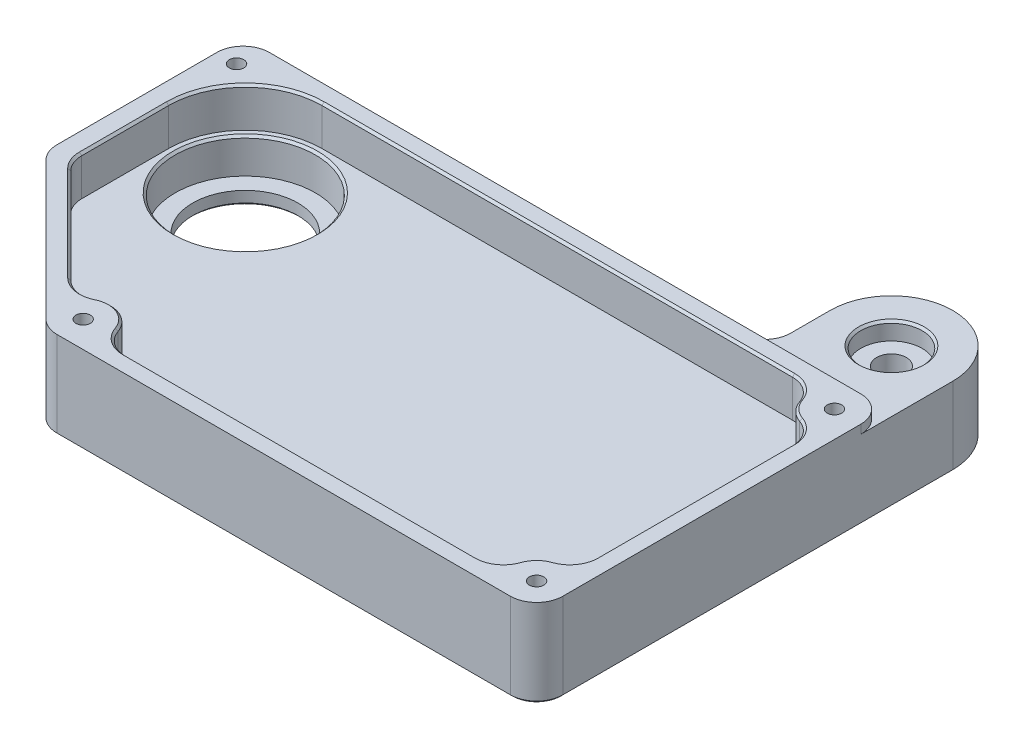
SolidWorks part; units mm, degrees
material "Alumina"
ref_plane "Plan de face" through (0, 0, 0) normal (0, 0, 1) x (1, 0, 0)
ref_plane "Plan de dessus" through (0, 0, 0) normal (0, 1, 0) x (1, 0, 0)
ref_plane "Plan de droite" through (0, 0, 0) normal (1, 0, 0) x (0, 0, -1)
sketch "Sketch2" plane through (0, 0, 0) normal (0, 1, 0) x (1, 0, 0)
  line L0 (-57, 40) -> (62, 40)
  line L1 (90, 55) -> (90, -40)
  line L10 (-22, -40) -> (90, -40)
  line L11 (62, 55) -> (62, 40)
  line L12 (-57, -5) -> (-22, -40)
  line L17 (-57, 40) -> (-57, -5)
  arc A9 (90, 55) -> (62, 55) centre (76, 55) ccw
  circle A10 centre (-35, 18.5) radius 12
  point P0 (-62, -40)
  dimension "D4" = 21.5
  dimension "D5" = 24
  dimension "D6" = 147
  dimension "D9" = 112
  dimension "D1" = 28
  dimension "D3" = 22
  dimension "D2" = 15
  dimension "D7" = 80
  dimension "D8" = 45
extrude "Boss-Extrude1" add sketch "Sketch2" along normal blind 20
fillet "Fillet1" radius 6 5 edges at (90, 10, 40) (62, 10, -40) (-22, 10, 40) (-57, 10, 5) (-57, 10, -40)
hole_wizard "Tap Drill for M4 Tap1" positions "Sketch5" profile "Sketch6" hole size "M4" standard "ISO"
sketch "Sketch5" plane through (0, 20, 0) normal (0, 1, 0) x (1, 0, 0)
  line L0 (-90, 10.5) -> (90, 10.5) construction
  line L1 (90, 55) -> (90, -34) construction
  line L2 (0, 40) -> (0, -40) construction
  line L3 (-51, 40) -> (56, 40) construction
  line L4 (-19.5147, -40) -> (84, -40) construction
  line L5 (90, 55) -> (90, -34) construction
  line L7 (84, 40) -> (-72.5, 40) construction
  line L11 (-57, 34) -> (-57, -2.5147) construction
  arc A10 (84, -40) -> (90, -34) centre (84, -34) ccw construction
  point P12 (-52.5, 34)
  point P16 (84, -34)
  point P18 (84, 34)
  point P108 (-19.5147, -34)
  dimension "D1" = 6
  dimension "D2" = 6
  dimension "D3" = 4.5
sketch "Sketch6" plane through (-19.5147, 20, 34) normal (1, 0, 0) x (0, 0, 1)
  line L0 (0, 0) -> (0, 13.9914)
  line L1 (0, 13.9914) -> (1.65, 13)
  line L2 (1.65, 13) -> (1.65, 0)
  line L5 (1.65, 0) -> (0, 0)
  line L10 (0, 13.9914) -> (-1.65, 13) construction
  line L11 (0, -6.35) -> (0, 107.95) construction
  dimension "Hole Dia." = 3.3
  dimension "Hole Depth" = 13
  dimension "Drill Angle" = 118
sketch "Sketch7" plane through (0, 20, 0) normal (0, 1, 0) x (1, 0, 0)
  line L0 (90, 55) -> (90, -34) construction
  line L1 (-52.5, 18.5) -> (-52.5, -1.3579)
  line L8 (66, 55) -> (66, 46)
  line L10 (-52.4142, -3.9289) -> (-20.9289, -35.4142)
  line L11 (-19.5147, -36) -> (84, -36)
  line L12 (86, -34) -> (86, 55)
  line L13 (56, 36) -> (-51, 36)
  line L14 (-50.7426, -5.6005) -> (-25.116, -31.2272)
  line L16 (-13.5934, -36) -> (78.0786, -36)
  line L17 (86, -28.0786) -> (86, 28.0786)
  line L18 (78.0786, 36) -> (-35, 36)
  line L26 (-53, 34) -> (-53, -2.5147)
  arc A0 (-52.5, -1.3579) -> (-50.7426, -5.6005) centre (-46.5, -1.3579) ccw
  circle A3 centre (84, 34) radius 1.65 construction
  arc A5 (-13.5934, -36) -> (-25.116, -31.2272) centre (-19.5147, -34) ccw
  arc A7 (-35, 36) -> (-52.5, 18.5) centre (-35, 18.5) ccw
  arc A10 (-51, 36) -> (-53, 34) centre (-51, 34) ccw
  arc A11 (84, -36) -> (86, -34) centre (84, -34) ccw
  arc A12 (86, 55) -> (66, 55) centre (76, 55) ccw
  arc A14 (-20.9289, -35.4142) -> (-19.5147, -36) centre (-19.5147, -34) ccw
  arc A22 (56, 36) -> (66, 46) centre (56, 46) ccw
  arc A24 (78.0786, 36) -> (86, 28.0786) centre (84, 34) ccw
  arc A26 (-53, -2.5147) -> (-52.4142, -3.9289) centre (-51, -2.5147) ccw
  arc A30 (86, -28.0786) -> (78.0786, -36) centre (84, -34) ccw
  dimension "D2" = 6
  dimension "D3" = 4
  dimension "D1" = 4
extrude "Cut-Extrude4" cut sketch "Sketch7" against normal blind 9
fillet "Fillet2" radius 6 6 edges at (86, 15.5, -28.0786) (78.0786, 15.5, -36) (86, 15.5, 28.0786) (78.0786, 15.5, 36) (-25.116, 15.5, 31.2272) (-13.5934, 15.5, 36)
sketch "Sketch8" plane through (0, 11, 0) normal (0, 1, 0) x (1, 0, 0)
  circle A0 centre (-35, 18.5) radius 16
  dimension "D1" = 32
extrude "Cut-Extrude5" cut sketch "Sketch8" against normal blind 8
hole_wizard "Tap Drill for M8 Tap1" positions "Sketch10" profile "Sketch11" hole size "M8" standard "ISO" end condition through all
sketch "Sketch10" plane through (0, 20, 0) normal (0, 1, 0) x (1, 0, 0)
  point P0 (76, 55)
sketch "Sketch11" plane through (76, 20, -55) normal (1, 0, 0) x (0, 0, 1)
  line L0 (0, 0) -> (0, 20)
  line L1 (0, 20) -> (3.4, 20)
  line L2 (3.4, 20) -> (3.4, 0)
  line L5 (3.4, 0) -> (0, 0)
  line L11 (0, -6.35) -> (0, 107.95) construction
  dimension "Thru Hole Dia." = 6.8
  dimension "Thru Hole Depth" = 20
sketch "Sketch12" plane through (0, 20, 0) normal (0, 1, 0) x (1, 0, 0)
  line L0 (84, 40) -> (50.8588, 40)
  line L2 (50.8588, 55) -> (50.8588, 40)
  line L3 (90, 34) -> (101.1412, 34)
  line L4 (101.1412, 55) -> (101.1412, 34)
  arc A1 (90, 34) -> (84, 40) centre (84, 34) ccw
  arc A2 (101.1412, 55) -> (50.8588, 55) centre (76, 55) ccw
extrude "Cut-Extrude6" cut sketch "Sketch12" against normal blind 2
sketch "Sketch13" plane through (0, 18, 0) normal (0, 1, 0) x (1, 0, 0)
  circle A0 centre (76, 55) radius 7
  dimension "D1" = 14
extrude "Cut-Extrude7" cut sketch "Sketch13" against normal blind 4
chamfer "Chamfer1" distance 0.5 angle 45 14 edges at (76, 0, -51.6) (-35, 0, -6.5) (32.2426, 0, 40) (-21.8108, 0, 39.5433) (88.2426, 0, 38.2426) (-39.5, 0, 22.5) (90, 0, -10.5) (-56.5433, 0, 4.8108) (76, 0, -69) (-57, 0, -15.7426) (62, 0, -50.5) (-55.2426, 0, -38.2426) (60.2426, 0, -41.7574) (2.5, 0, -40)
chamfer "Chamfer2" distance 0.5 angle 45 18 edges at (-35, 11, -2.5) (79.5806, 20, 29.5806) (84.8865, 20, 25.9032) (75.9032, 20, 34.8865) (86, 20, 0) (32.2426, 20, 36) (84.8865, 20, -25.9032) (-11.4179, 20, 34.8865) (79.5806, 20, -29.5806) (-17.1229, 20, 28.2258) (75.9032, 20, -34.8865) (-25.8669, 20, 28.9015) (18.7107, 20, -36) (-39.9294, 20, 16.4137) (-47.3744, 20, -30.8744) (-52.0433, 20, 3.654) (-52.5, 20, -8.5711) (76, 18, -48)
